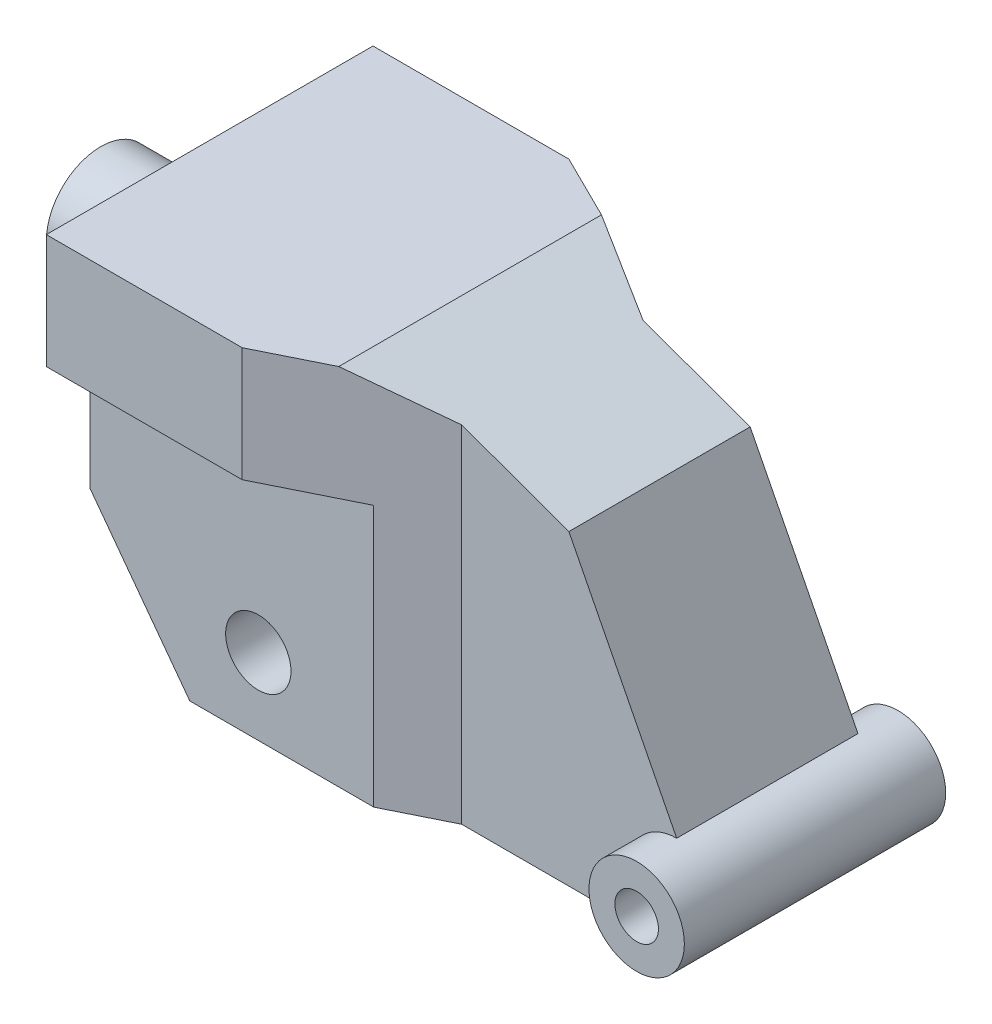
SolidWorks part; units mm, degrees
ref_plane "前视基准面" through (0, 0, 0) normal (0, 0, 1) x (1, 0, 0)
ref_plane "上视基准面" through (0, 0, 0) normal (0, 1, 0) x (1, 0, 0)
ref_plane "右视基准面" through (0, 0, 0) normal (1, 0, 0) x (0, 0, -1)
sketch "草图1" plane through (0, 0, 0) normal (0, 0, 1) x (1, 0, 0)
  line L0 (-119.6, 172.5014) -> (0, 172.5014)
  line L1 (0, 172.5014) -> (86.9794, 141.0238)
  line L2 (86.9794, 141.0238) -> (136.4804, 43.8)
  line L3 (136.4804, 43.8) -> (136.4804, 0)
  line L4 (136.4804, 0) -> (-73.7196, 0)
  line L5 (-73.7196, 0) -> (-119.6, 61.7014)
  line L6 (-119.6, 61.7014) -> (-119.6, 172.5014)
  line L7 (0, 0) -> (-223.2596, 0) construction
  dimension "D1" = 119.6
  dimension "D2" = 92.5
  dimension "D3" = 109.1
  dimension "D4" = 43.8
  dimension "D5" = 210.2
  dimension "D6" = 76.89
  dimension "D7" = 110.8
  dimension "D8" = 0
extrude "凸台-拉伸1" add sketch "草图1" along normal mid plane 150
sketch "草图2" plane through (0, 0, 0) normal (0, 1, 0) x (1, 0, 0)
  line L0 (-144.6, 55) -> (41.2, 55)
  line L1 (41.2, 55) -> (41.2, 112.3)
  line L2 (41.2, 112.3) -> (-144.6, 112.3)
  line L3 (-144.6, 112.3) -> (-144.6, 55)
  line L4 (0, 0) -> (168.4303, 0) construction
  line L5 (-144.6, -112.3) -> (-144.6, -55)
  line L6 (41.2, -112.3) -> (-144.6, -112.3)
  line L7 (41.2, -55) -> (41.2, -112.3)
  line L8 (-144.6, -55) -> (41.2, -55)
  line L10 (-119.6, -75) -> (-119.6, 75) construction
  dimension "D1" = 185.8
  dimension "D2" = 57.3
  dimension "D3" = 110
  dimension "D4" = 25
extrude "切除-拉伸2" cut sketch "草图2" along normal blind 120
sketch "草图3" plane through (0, 172.5014, 0) normal (0, 1, 0) x (1, 0, 0)
  line L0 (-64.8373, 92.4203) -> (245.3627, 92.4203)
  line L1 (245.3627, 92.4203) -> (245.3627, 41.6203)
  line L2 (245.3627, 41.6203) -> (37.7766, 41.6203)
  line L3 (37.7766, 41.6203) -> (-64.8373, 92.4203)
  line L4 (0, 0) -> (272.7146, 0) construction
  line L5 (37.7766, -41.6203) -> (-64.8373, -92.4203)
  line L6 (245.3627, -41.6203) -> (37.7766, -41.6203)
  line L7 (245.3627, -92.4203) -> (245.3627, -41.6203)
  line L8 (-64.8373, -92.4203) -> (245.3627, -92.4203)
  dimension "D1" = 310.2
  dimension "D2" = 114.5
  dimension "D3" = 50.8
extrude "切除-拉伸3" cut sketch "草图3" against normal blind 400
sketch "草图5" plane through (0, 0, 0) normal (0, 0, 1) x (1, 0, 0)
  line L0 (136.4804, 43.8) -> (136.4804, 0) construction
  circle A0 centre (136.4804, 21.9) radius 21.9
  dimension "D1" = 43.8
extrude "凸台-拉伸2" add sketch "草图5" along normal mid plane 120
sketch "草图6" plane through (0, 0, 60) normal (0, 0, 1) x (1, 0, 0)
  circle A0 centre (136.4804, 21.9) radius 10
  dimension "D1" = 20
extrude "切除-拉伸4" cut sketch "草图6" against normal blind 200
sketch "草图7" plane through (-119.6, 0, 0) normal (-1, 0, 0) x (0, 0, 1)
  line L0 (-75, 172.5014) -> (75, 120) construction
sketch "草图8" plane through (0, 0, 55) normal (0, 0, 1) x (1, 0, 0)
  line L0 (10.7502, 120) -> (10.7502, 0) construction
  line L1 (10.7502, 0) -> (-73.7196, 0) construction
  circle A0 centre (-42.2498, 35) radius 15
  point P6 (0, 0)
  dimension "D1" = 30
  dimension "D2" = 53
  dimension "D3" = 35
extrude "切除-拉伸5" cut sketch "草图8" against normal through all both and the other way through all
sketch "草图9" plane through (-119.6, 0, 0) normal (-1, 0, 0) x (0, 0, 1)
  line L0 (-75, 120) -> (-55, 120) construction
  circle A0 centre (0, 120) radius 25
  dimension "D1" = 50
  dimension "D2" = 0
extrude "凸台-拉伸3" add sketch "草图9" along normal blind 50
